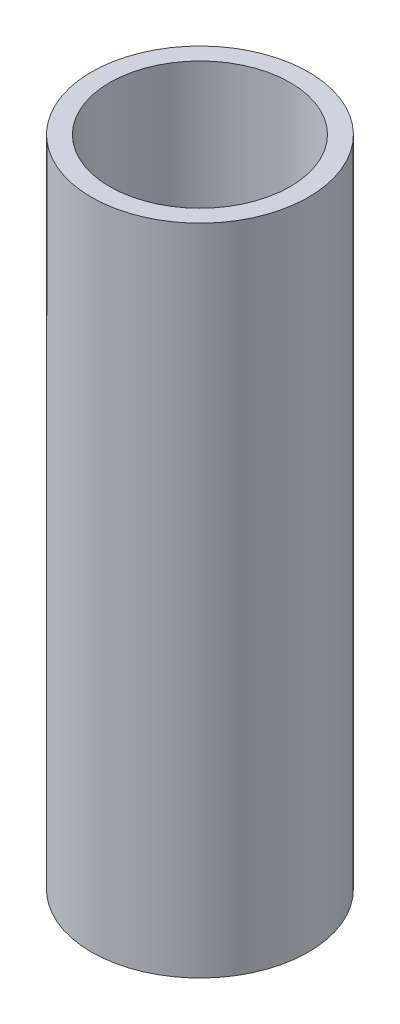
SolidWorks part; units mm, degrees
material "Plain Carbon Steel"
ref_plane "Front Plane" through (0, 0, 0) normal (0, 0, 1) x (1, 0, 0)
ref_plane "Top Plane" through (0, 0, 0) normal (0, 1, 0) x (1, 0, 0)
ref_plane "Right Plane" through (0, 0, 0) normal (1, 0, 0) x (0, 0, -1)
sketch "Sketch1" plane through (0, 0, 0) normal (0, 1, 0) x (1, 0, 0)
  circle A0 centre (0, 0) radius 21.082
  circle A1 centre (0, 0) radius 17.526
  dimension "D1" = 42.164
  dimension "D2" = 35.052
extrude "Boss-Extrude1" add sketch "Sketch1" along normal blind 127
